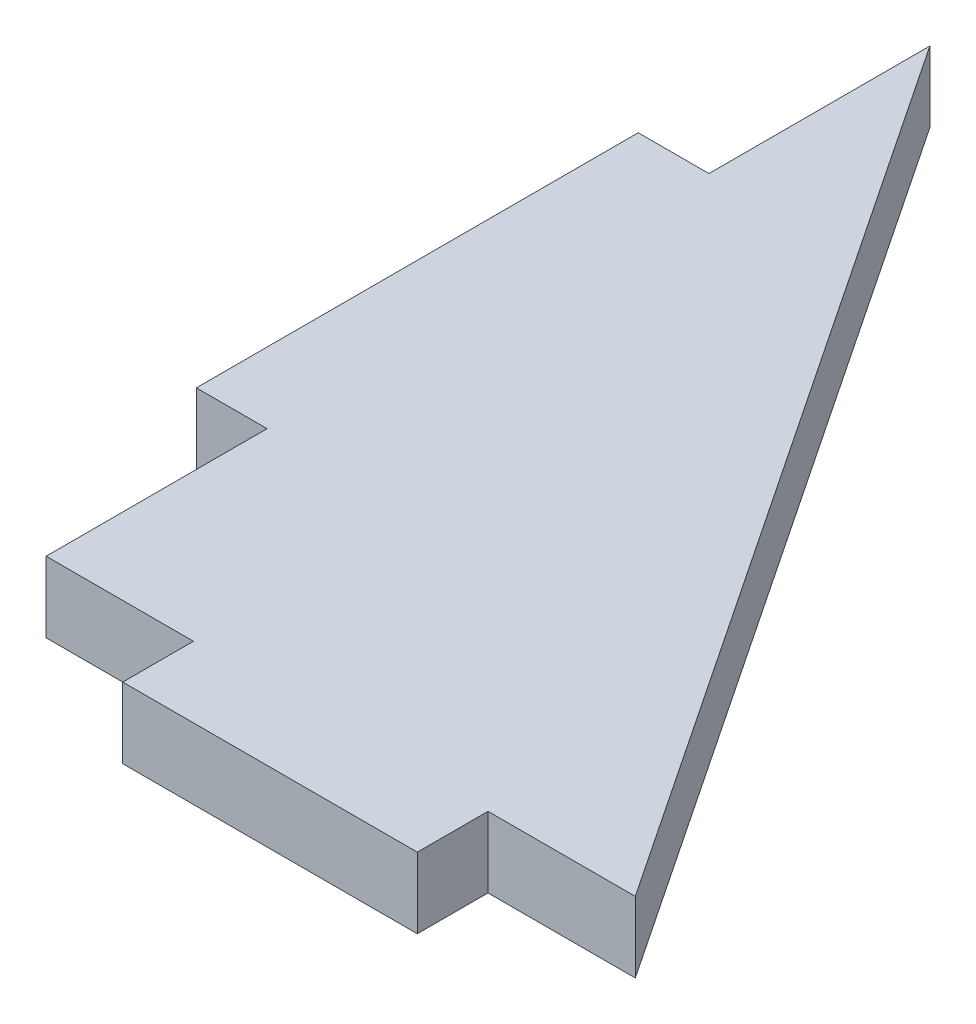
SolidWorks part; units mm, degrees
ref_plane "Front Plane" through (0, 0, 0) normal (0, 0, 1) x (1, 0, 0)
ref_plane "Top Plane" through (0, 0, 0) normal (0, 1, 0) x (1, 0, 0)
ref_plane "Right Plane" through (0, 0, 0) normal (1, 0, 0) x (0, 0, -1)
sketch "Sketch1" plane through (0, 0, 0) normal (0, 1, 0) x (1, 0, 0)
  line L0 (0, 0) -> (100, 0)
  line L1 (-55, 0) -> (55, 0) construction
  line L2 (0, 0) -> (0, 150)
  line L3 (0, -55) -> (0, 55) construction
  line L4 (0, 150) -> (100, 0)
  line L6 (25, 12) -> (75, 12)
  line L7 (25, 12) -> (25, -12)
  line L8 (25, -12) -> (75, -12)
  line L9 (75, 12) -> (75, -12)
  line L10 (25, 12) -> (75, -12) construction
  line L11 (25, -12) -> (75, 12) construction
  line L12 (-12, 112.5) -> (12, 112.5)
  line L13 (-12, 112.5) -> (-12, 37.5)
  line L14 (-12, 37.5) -> (12, 37.5)
  line L15 (12, 112.5) -> (12, 37.5)
  line L16 (-12, 112.5) -> (12, 37.5) construction
  line L17 (-12, 37.5) -> (12, 112.5) construction
  point P5 (50, 0)
  point P13 (0, 75)
  dimension "D1" = 150
  dimension "D2" = 100
  dimension "D3" = 24
  dimension "D4" = 50
  dimension "D5" = 25
  dimension "D6" = 24
  dimension "D7" = 75
  dimension "D8" = 37.5
extrude "Boss-Extrude1" add sketch "Sketch1" along normal blind 12 contours L13 L14 L2 L12 | L12 L15 L14 L2 L0 L7 L6 L9 L4 | L9 L0 L7 L8 | L9 L6 L7 L0 | L15 L12 L2 L14
